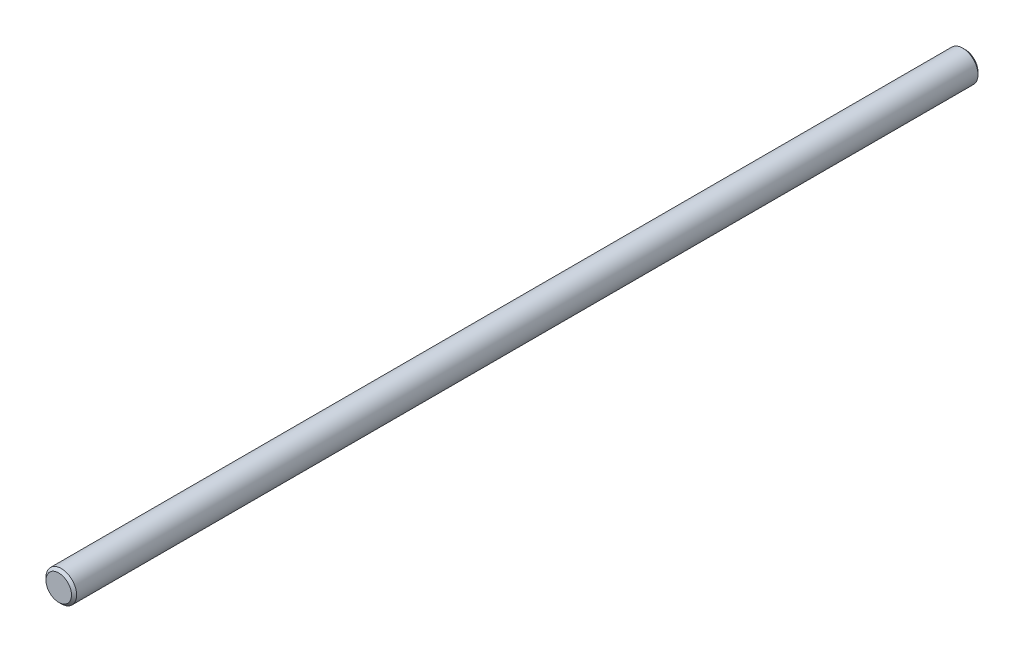
SolidWorks part; units mm, degrees
material "Acciaio inossidabile al cromo"
ref_plane "Piano frontale" through (0, 0, 0) normal (0, 0, 1) x (1, 0, 0)
ref_plane "Piano superiore" through (0, 0, 0) normal (0, 1, 0) x (1, 0, 0)
ref_plane "Piano destro" through (0, 0, 0) normal (1, 0, 0) x (0, 0, -1)
sketch "Schizzo1" plane through (0, 0, 0) normal (0, 0, 1) x (1, 0, 0)
  circle A0 centre (0, 0) radius 6
  dimension "D1" = 12
extrude "Estrusione-Estrusione1" add sketch "Schizzo1" along normal blind 355
chamfer "Smusso1" distance 1 angle 45 2 edges at (6, 0, 355) (6, 0, 0)
